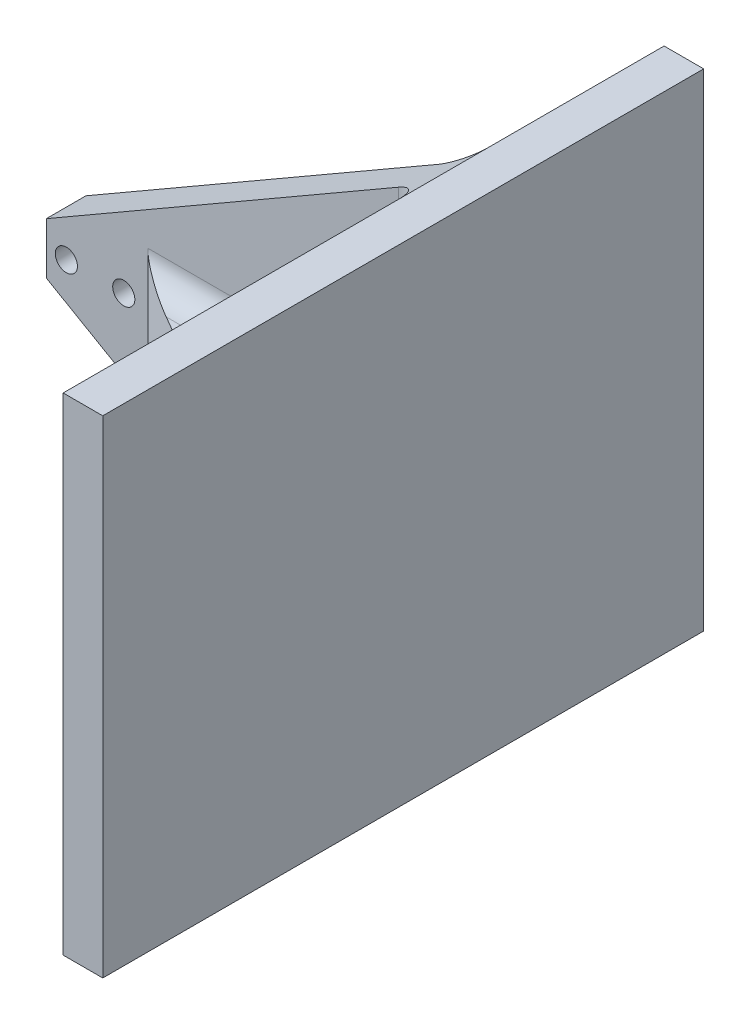
SolidWorks part; units mm, degrees
ref_plane "Front Plane" through (0, 0, 0) normal (0, 0, 1) x (1, 0, 0)
ref_plane "Top Plane" through (0, 0, 0) normal (0, 1, 0) x (1, 0, 0)
ref_plane "Right Plane" through (0, 0, 0) normal (1, 0, 0) x (0, 0, -1)
sketch "Sketch1" plane through (0, 0, 0) normal (0, 0, 1) x (1, 0, 0)
  line L0 (0, 13) -> (0, 0) construction
  line L2 (0, 0) -> (0, 13) construction
  line L4 (-24.634, 0) -> (-24.634, 13)
  line L5 (0, 6.5) -> (-5.067, 6.5) construction
  line L6 (-19.567, 6.5) -> (-24.634, 6.5) construction
  line L7 (-24.634, 0) -> (70.616, -54.9926)
  line L8 (70.616, -54.9926) -> (70.616, 67.9926)
  line L9 (70.616, 67.9926) -> (-24.634, 13)
  line L10 (70.616, 6.5) -> (-24.634, 6.5) construction
  dimension "D1" = 95.25
  dimension "D2" = 60
extrude "Boss-Extrude1" add sketch "Sketch1" along normal blind 10
sketch "Sketch3" plane through (0, 13, 0) normal (0, 1, 0) x (1, 0, 0)
  line L0 (70.616, -10) -> (-24.634, -10) construction
  line L3 (70.616, -50.1928) -> (70.616, -10)
  line L4 (1, -10) -> (70.616, -50.1928)
  line L10 (1, -10) -> (70.616, -10)
  line L52 (0, 13) -> (0, 0) construction
  dimension "D1" = 60
  dimension "D2" = 1
extrude "Boss-Extrude2" add sketch "Sketch3" against normal up to surface (13 mm away)
sketch "Sketch4" plane through (70.616, 0, 0) normal (1, 0, 0) x (0, 0, -1)
  line L0 (-10, 67.9926) -> (0, 67.9926) construction
  line L1 (-100.9928, 67.9926) -> (50.8, 67.9926)
  line L2 (-100.9928, 67.9926) -> (-100.9928, -54.9926)
  line L3 (-100.9928, -54.9926) -> (50.8, -54.9926)
  line L4 (50.8, 67.9926) -> (50.8, -54.9926)
  line L5 (-10, -54.9926) -> (0, -54.9926) construction
  line L6 (0, -54.9926) -> (0, 67.9926) construction
  line L8 (-50.1928, 0) -> (-50.1928, 13) construction
  dimension "D1" = 50.8
  dimension "D2" = 50.8
extrude "Boss-Extrude3" add sketch "Sketch4" along normal blind 10
sketch "Sketch5" plane through (0, 0, 0) normal (0, 0, -1) x (-1, 0, 0)
  circle A0 centre (5.067, 6.5) radius 2.8
  circle A1 centre (19.567, 6.5) radius 2.8
  dimension "D1" = 5.6
  dimension "D2" = 5.6
extrude "Cut-Extrude1" cut sketch "Sketch5" against normal through all
fillet "Fillet1" radius 6.35 8 edges at (70.616, 6.5, 0) (70.616, 40.4963, 10) (70.616, 13, 30.0964) (70.616, 6.5, 50.1928) (70.616, 0, 30.0964) (70.616, -27.4963, 10) (35.808, 0, 10) (35.808, 13, 10)
sketch "Sketch6" plane through (0, 0, 0) normal (0, 0, -1) x (-1, 0, 0)
  line L0 (80, 13) -> (0, 13) construction
  line L1 (0, 0) -> (80, 0) construction
  line L2 (24.634, 13) -> (0, 13)
  line L3 (0, 0) -> (24.634, 0)
  line L4 (24.634, 13) -> (24.634, 0)
  line L5 (0, 13) -> (0, 0)
split line "Split Line1"
ref_point "Point1"
